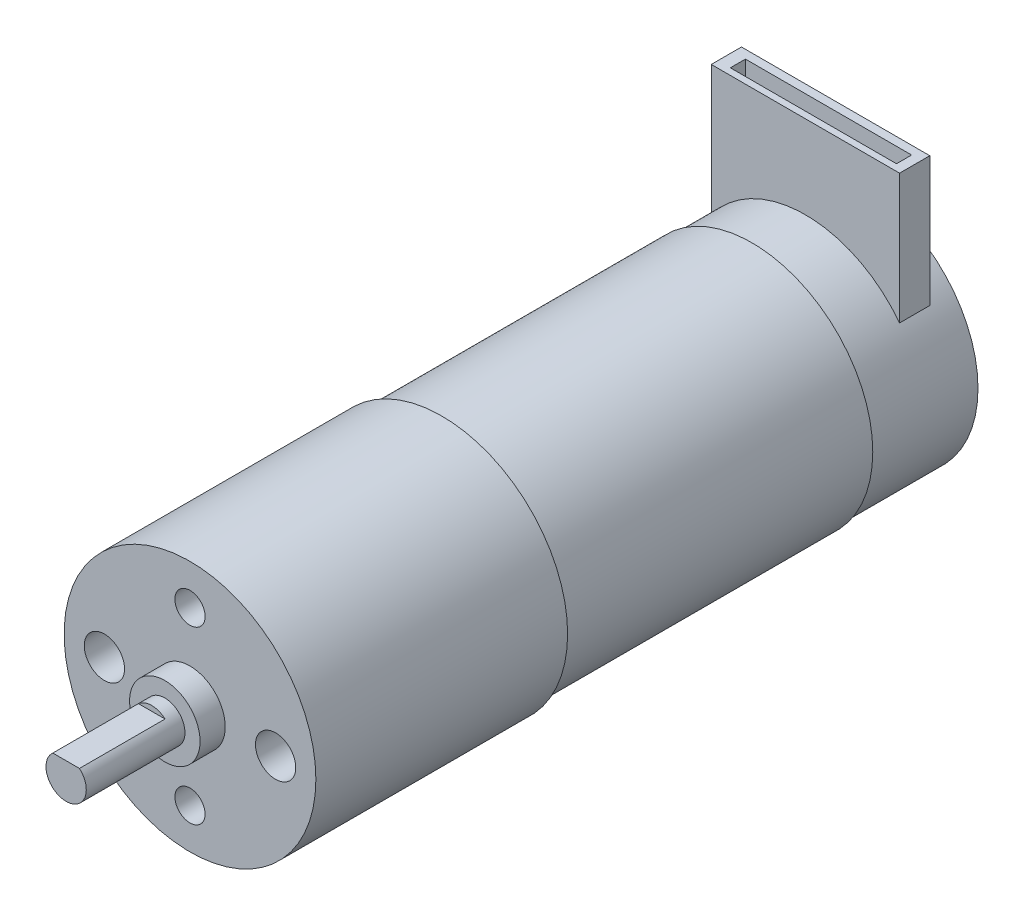
SolidWorks part; units mm, degrees
material "1060 Alloy"
ref_plane "Front Plane" through (0, 0, 0) normal (0, 0, 1) x (1, 0, 0)
ref_plane "Top Plane" through (0, 0, 0) normal (0, 1, 0) x (1, 0, 0)
ref_plane "Right Plane" through (0, 0, 0) normal (1, 0, 0) x (0, 0, -1)
sketch "Sketch1" plane through (0, 0, 0) normal (0, 0, 1) x (1, 0, 0)
  circle A0 centre (0, 0) radius 12
  dimension "D1" = 24
extrude "Boss-Extrude1" add sketch "Sketch1" along normal blind 30.8
sketch "Sketch2" plane through (0, 0, 30.8) normal (0, 0, 1) x (1, 0, 0)
  circle A0 centre (0, 0) radius 12.5
  dimension "D1" = 25
extrude "Boss-Extrude2" add sketch "Sketch2" along normal blind 25
sketch "Sketch3" plane through (0, 0, 55.8) normal (0, 0, 1) x (1, 0, 0)
  circle A0 centre (0, 0) radius 3.5
  dimension "D1" = 7
extrude "Boss-Extrude3" add sketch "Sketch3" along normal blind 2.5
sketch "Sketch4" plane through (0, 0, 58.3) normal (0, 0, 1) x (1, 0, 0)
  circle A0 centre (0, 0) radius 2
  dimension "D1" = 4
extrude "Boss-Extrude4" add sketch "Sketch4" along normal blind 9.8
sketch "Sketch5" plane through (0, 0, 68.1) normal (0, 0, 1) x (1, 0, 0)
  line L0 (0, 0) -> (0, 1.5) construction
  line L1 (0, 1.5) -> (1.3229, 1.5)
  line L2 (1.3229, 1.5) -> (-1.3229, 1.5)
  circle A0 centre (0, 0) radius 2 construction
  circle M1 centre (0, 0) radius 2
  dimension "D1" = 1.5
extrude "Cut-Extrude1" cut sketch "Sketch5" against normal blind 8.5 contours L2 L1 M1
sketch "Sketch6" plane through (0, 0, 0) normal (0, 0, -1) x (-1, 0, 0)
  circle A0 centre (0, 0) radius 11.75
  dimension "D1" = 23.5
extrude "Boss-Extrude5" add sketch "Sketch6" along normal blind 10.7
sketch "Sketch7" plane through (0, 0, 0) normal (0, 1, 0) x (1, 0, 0)
  line L1 (9.3497, 8.3124) -> (-9.3497, 8.3124)
  line L2 (9.3497, 8.3124) -> (9.3497, 5.3124)
  line L3 (9.3497, 5.3124) -> (-9.3497, 5.3124)
  line L4 (-9.3497, 8.3124) -> (-9.3497, 5.3124)
  line L5 (9.3497, 8.3124) -> (-9.3497, 5.3124) construction
  line L6 (9.3497, 5.3124) -> (-9.3497, 8.3124) construction
  point P0 (0, 6.8124)
  dimension "D1" = 18.6994
  dimension "D2" = 3
extrude "Boss-Extrude6" add sketch "Sketch7" along normal blind 20
sketch "Sketch8" plane through (0, 0, 55.8) normal (0, 0, 1) x (1, 0, 0)
  line L0 (0, 0) -> (0, -8.5) construction
  circle A0 centre (0, -8.5) radius 1.5
  dimension "D2" = 3
  dimension "D1" = 8.5
extrude "Cut-Extrude2" cut sketch "Sketch8" against normal blind 10
mirror "Mirror1" about plane through (0, 0, 0) normal (0, 1, 0) of "Cut-Extrude2"
sketch "Sketch9" plane through (0, 0, 55.8) normal (0, 0, 1) x (1, 0, 0)
  line L0 (0, 0) -> (-8.5, 0) construction
  circle A0 centre (-8.5, 0) radius 2
  dimension "D2" = 4
  dimension "D1" = 8.5
extrude "Cut-Extrude3" cut sketch "Sketch9" against normal blind 10
mirror "Mirror3" about plane through (0, 0, 0) normal (1, 0, 0) of "Cut-Extrude3"
sketch "Sketch10" plane through (0, 20, 0) normal (0, 1, 0) x (1, 0, 0)
  line L1 (8.3873, 7.4684) -> (-8.1127, 7.4684)
  line L2 (8.3873, 7.4684) -> (8.3873, 5.9684)
  line L3 (8.3873, 5.9684) -> (-8.1127, 5.9684)
  line L4 (-8.1127, 7.4684) -> (-8.1127, 5.9684)
  line L5 (8.3873, 7.4684) -> (-8.1127, 5.9684) construction
  line L6 (8.3873, 5.9684) -> (-8.1127, 7.4684) construction
  point P0 (0.1373, 6.7184)
  dimension "D1" = 16.5
  dimension "D2" = 1.5
extrude "Cut-Extrude4" cut sketch "Sketch10" against normal blind 10
